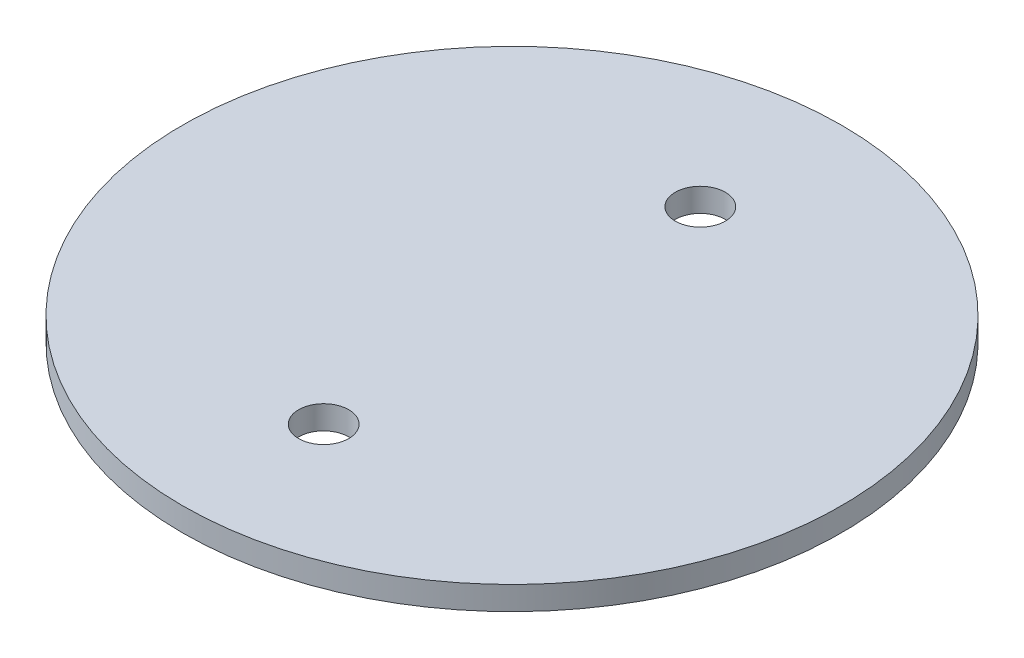
SolidWorks part; units mm, degrees
material "A-Glass Fiber"
ref_plane "Front Plane" through (0, 0, 0) normal (0, 0, 1) x (1, 0, 0)
ref_plane "Top Plane" through (0, 0, 0) normal (0, 1, 0) x (1, 0, 0)
ref_plane "Right Plane" through (0, 0, 0) normal (1, 0, 0) x (0, 0, -1)
sketch "Sketch1" plane through (0, 0, 0) normal (0, 1, 0) x (1, 0, 0)
  circle A0 centre (0, 0) radius 44.45
  dimension "D1" = 88.9
extrude "Boss-Extrude1" add sketch "Sketch1" along normal mid plane 3.175
sketch "Sketch2" plane through (0, 1.5875, 0) normal (0, 1, 0) x (1, 0, 0)
  line L0 (0, 25.4) -> (0, -25.4) construction
  point P2 (0, 0)
  dimension "D1" = 25.4
sketch "Sketch3" plane through (0, 1.5875, 0) normal (0, 1, 0) x (1, 0, 0)
  point P0 (0, 25.4)
  point P3 (0, -25.4)
hole_wizard "1/4 Clearance Hole1" positions "Sketch3" profile "Sketch4" hole size "1/4" standard "ANSI Inch" end condition through all
sketch "Sketch4" plane through (0, 1.5875, -25.4) normal (1, 0, 0) x (0, 0, 1)
  line L0 (0, 0) -> (0, 3.175)
  line L1 (0, 3.175) -> (3.3782, 3.175)
  line L2 (3.3782, 3.175) -> (3.3782, 0)
  line L5 (3.3782, 0) -> (0, 0)
  line L11 (0, -6.35) -> (0, 107.95) construction
  dimension "Thru Hole Dia." = 6.7564
  dimension "Thru Hole Depth" = 3.175
